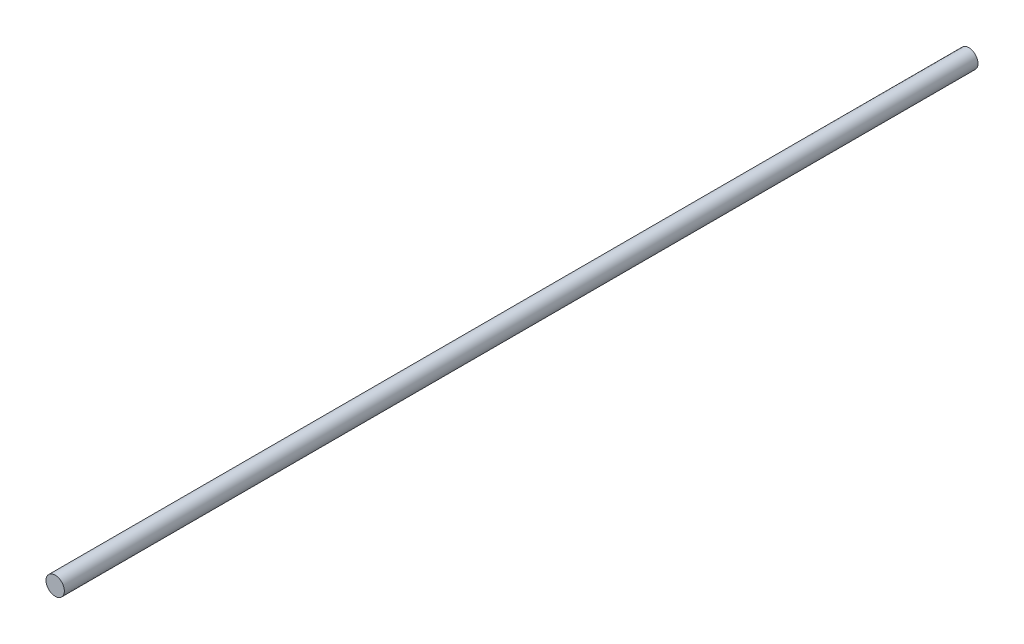
SolidWorks part; units mm, degrees
material "Liga 1060"
ref_plane "Plano frontal" through (0, 0, 0) normal (0, 0, 1) x (1, 0, 0)
ref_plane "Plano superior" through (0, 0, 0) normal (0, 1, 0) x (1, 0, 0)
ref_plane "Plano direito" through (0, 0, 0) normal (1, 0, 0) x (0, 0, -1)
sketch "Esboço1" plane through (0, 0, 0) normal (0, 0, 1) x (1, 0, 0)
  circle A0 centre (0, 0) radius 3.97
  dimension "D1" = 7.94
extrude "Ressalto-extrusão1" add sketch "Esboço1" along normal mid plane 395
